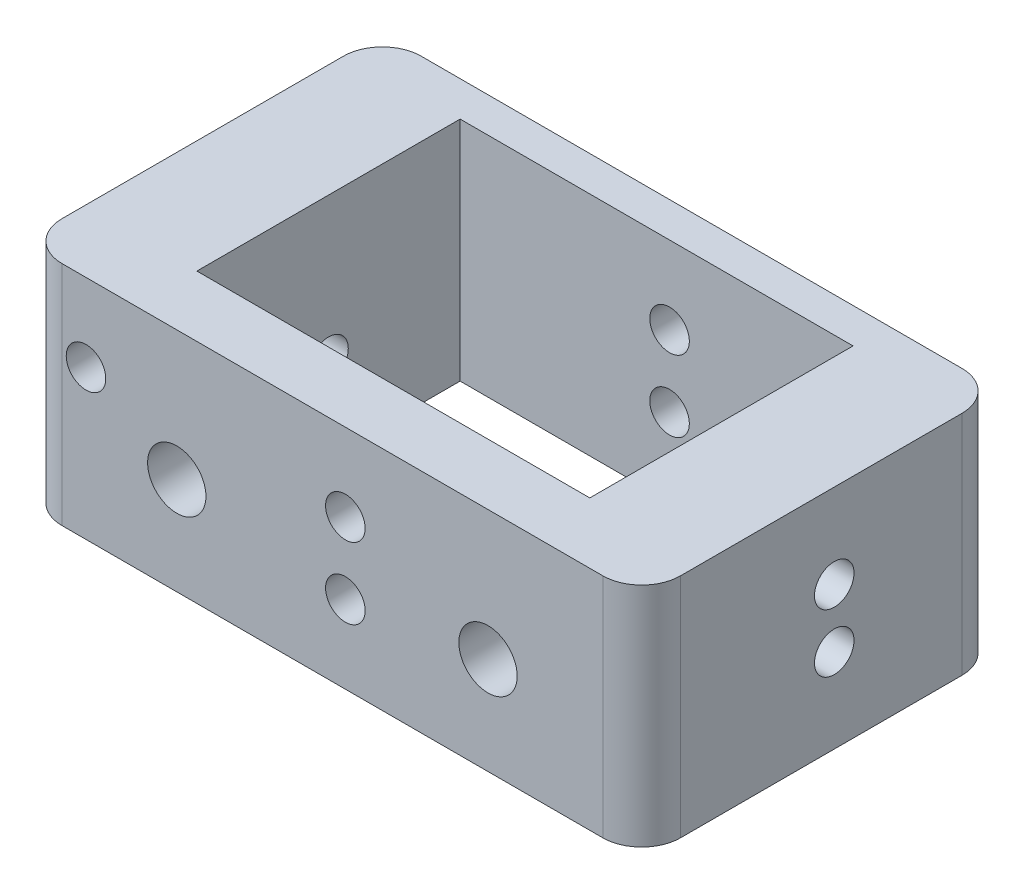
SolidWorks part; units mm, degrees
material "ABS"
ref_plane "前视基准面" through (0, 0, 0) normal (0, 0, 1) x (1, 0, 0)
ref_plane "上视基准面" through (0, 0, 0) normal (0, 1, 0) x (1, 0, 0)
ref_plane "右视基准面" through (0, 0, 0) normal (1, 0, 0) x (0, 0, -1)
other "Configuration Table"
sketch "草图1" plane through (0, 0, 0) normal (0, 1, 0) x (1, 0, 0)
  line L1 (-23.85, -13.85) -> (23.85, -13.85)
  line L2 (-23.85, -13.85) -> (-23.85, 13.85)
  line L3 (-23.85, 13.85) -> (23.85, 13.85)
  line L4 (23.85, -13.85) -> (23.85, 13.85)
  line L5 (-23.85, -13.85) -> (23.85, 13.85) construction
  line L6 (-23.85, 13.85) -> (23.85, -13.85) construction
  line L7 (-15.15, -10.15) -> (15.15, -10.15) construction
  line L8 (-15.15, -10.15) -> (-15.15, 10.15) construction
  line L9 (-15.15, 10.15) -> (15.15, 10.15) construction
  line L10 (15.15, -10.15) -> (15.15, 10.15) construction
  line L11 (-15.15, -10.15) -> (15.15, 10.15) construction
  line L12 (-15.15, 10.15) -> (15.15, -10.15) construction
  line L13 (-15.15, -9.15) -> (15.15, -9.15)
  line L14 (-15.15, -9.15) -> (-15.15, 11.15)
  line L15 (-15.15, 11.15) -> (15.15, 11.15)
  line L16 (15.15, -9.15) -> (15.15, 11.15)
  line L17 (-15.15, -9.15) -> (15.15, 11.15) construction
  line L18 (-15.15, 11.15) -> (15.15, -9.15) construction
  point P0 (0, 0)
  point P6 (0, 0)
  point P12 (0, 1)
  dimension "D1" = 20.3
  dimension "D2" = 27.7
  dimension "D3" = 30.3
  dimension "D4" = 47.7
  dimension "D5" = 20.3
  dimension "D6" = 30.3
  dimension "D7" = 1
extrude "凸台-拉伸1" add sketch "草图1" along normal mid plane 17.5
sketch "草图2" plane through (0, 0, -13.85) normal (0, 0, -1) x (-1, 0, 0)
  circle A0 centre (-1, 2.75) radius 1.525
  dimension "D1" = 3.05
extrude "切除-拉伸1" cut sketch "草图2" against normal through all
sketch "草图3" plane through (23.85, 0, 0) normal (1, 0, 0) x (0, 0, -1)
  line L0 (-13.85, 8.75) -> (13.85, 8.75) construction
  circle A0 centre (1, -2.25) radius 1.525
  dimension "D1" = 11
  dimension "D2" = 3.05
  dimension "D3" = 1
extrude "切除-拉伸2" cut sketch "草图3" against normal through all
sketch "草图4" plane through (0, 0, -13.85) normal (0, 0, -1) x (-1, 0, 0)
  circle A0 centre (19, 2.75) radius 1.525
  dimension "D1" = 3.05
extrude "切除-拉伸3" cut sketch "草图4" against normal through all
sketch "草图5" plane through (0, 0, 13.85) normal (0, 0, 1) x (1, 0, 0)
  circle A0 centre (-12, -1.25) radius 2.25
  circle A1 centre (12, -1.25) radius 2.25
  dimension "D1" = 4.5
extrude "切除-拉伸4" cut sketch "草图5" against normal blind 5
sketch "草图7" plane through (0, 0, -13.85) normal (0, 0, -1) x (-1, 0, 0)
  line L0 (-1, 2.75) -> (-1, -2.75) construction
  line L1 (0, 0) -> (-1, 0) construction
  circle A0 centre (-1, -2.75) radius 1.525
  dimension "D2" = 3.05
  dimension "D1" = 2.75
extrude "切除-拉伸6" cut sketch "草图7" against normal through all both and the other way through all
sketch "草图8" plane through (23.85, 0, 0) normal (1, 0, 0) x (0, 0, -1)
  line L0 (1, 2.25) -> (1, -271.25) construction
  circle A0 centre (1, 2.25) radius 1.525
  dimension "D2" = 3.05
  dimension "D1" = 2.25
extrude "切除-拉伸7" cut sketch "草图8" against normal up to next
fillet "圆角2" radius 3 4 edges at (23.85, 0, 13.85) (-23.85, 0, -13.85) (23.85, 0, -13.85) (-23.85, 0, 13.85)
